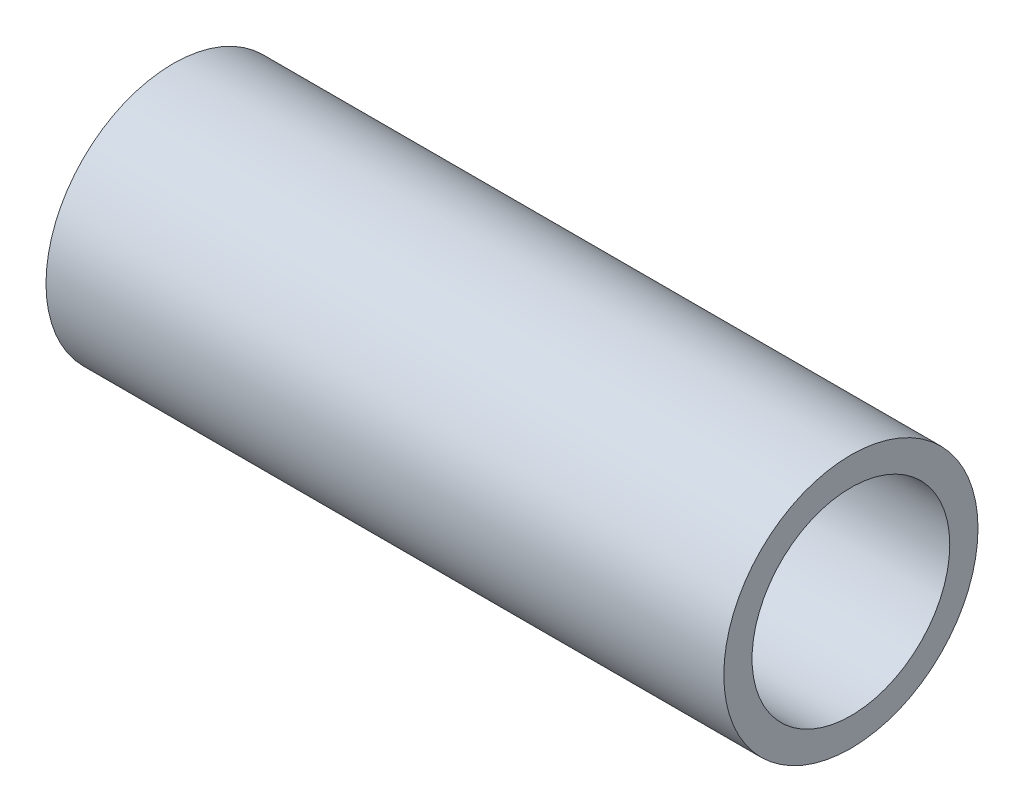
SolidWorks part; units mm, degrees
ref_plane "Front Plane" through (0, 0, 0) normal (0, 0, 1) x (1, 0, 0)
ref_plane "Top Plane" through (0, 0, 0) normal (0, 1, 0) x (1, 0, 0)
ref_plane "Right Plane" through (0, 0, 0) normal (1, 0, 0) x (0, 0, -1)
sketch "Sketch1" plane through (0, 0, 0) normal (1, 0, 0) x (0, 0, -1)
  circle A0 centre (0, 0) radius 9
  circle A1 centre (0, 0) radius 7
  dimension "D1" = 18
  dimension "D2" = 14
extrude "Boss-Extrude1" add sketch "Sketch1" along normal mid plane 48
